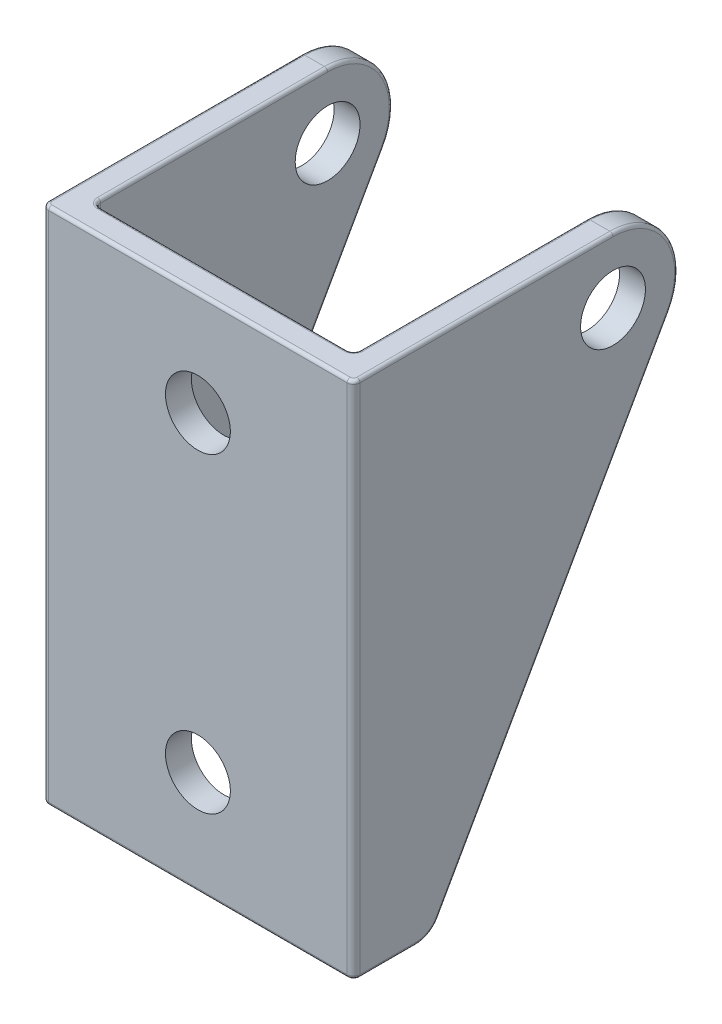
SolidWorks part; units mm, degrees
ref_plane "Front Plane" through (0, 0, 0) normal (0, 0, 1) x (1, 0, 0)
ref_plane "Top Plane" through (0, 0, 0) normal (0, 1, 0) x (1, 0, 0)
ref_plane "Right Plane" through (0, 0, 0) normal (1, 0, 0) x (0, 0, -1)
sketch "Sketch1" plane through (0, 0, 0) normal (0, 1, 0) x (1, 0, 0)
  line L0 (12, -1.5) -> (12, 23)
  line L1 (-11.5, -2) -> (11.5, -2)
  line L2 (-12, -1.5) -> (-12, 23)
  line L5 (12, 23) -> (10, 23)
  line L6 (10, 23) -> (10, 0.5)
  line L7 (9.5, 0) -> (-9.5, 0)
  line L8 (-10, 0.5) -> (-10, 23)
  line L9 (-10, 23) -> (-12, 23)
  line L10 (0, 0) -> (0, -2) construction
  arc A4 (11.5, -2) -> (12, -1.5) centre (11.5, -1.5) ccw
  arc A5 (10, 0.5) -> (9.5, 0) centre (9.5, 0.5) cw
  arc A6 (-9.5, 0) -> (-10, 0.5) centre (-9.5, 0.5) cw
  arc A7 (-11.5, -2) -> (-12, -1.5) centre (-11.5, -1.5) cw
  point P0 (0, 0)
  point P17 (12, 23)
  point P22 (12, -2)
  point P25 (10, 0)
  point P28 (-10, 0)
  point P36 (0, 0)
  dimension "D5" = 0.5
  dimension "D1" = 2
  dimension "D3" = 20
  dimension "D4" = 25
extrude "Boss-Extrude1" add sketch "Sketch1" along normal blind 40
sketch "Sketch2" plane through (-12, 0, 0) normal (-1, 0, 0) x (0, 0, 1)
  line L0 (-23, 40) -> (1.5, 40) construction
  line L1 (-22.3551, 32.5437) -> (-4.5739, 1.0175)
  line L4 (-23, 0) -> (1.5, 0) construction
  line L5 (-18, 40) -> (2, 40)
  line L6 (2, 40) -> (2, 0)
  line L7 (2, 0) -> (-2.8318, 0)
  line L10 (-23, 40) -> (-23, 0) construction
  arc A0 (-18, 40) -> (-22.3551, 32.5437) centre (-18, 35) ccw
  arc A1 (-4.5739, 1.0175) -> (-2.8318, 0) centre (-2.8318, 2) ccw
  point P19 (-4, 0)
  dimension "D1" = 5
  dimension "D3" = 2
  dimension "D2" = 6
extrude "Cut-Extrude1" cut sketch "Sketch2" against normal blind 30 flip side to cut
fillet "Fillet1" radius 0.25 32 edges at (10, 0, -1.6659) (-10, 0, -1.6659) (-9.8536, 0, -0.1464) (0, 0, 0) (12, 16.7806, -13.4645) (12, 37.5218, -22.3175) (12, 40, -8.25) (11.8536, 40, 1.8536) (0, 40, 2) (-11.8536, 40, 1.8536) (-12, 40, -8.25) (-12, 37.5218, -22.3175) (12, 0, -0.6659) (11.8536, 0, 1.8536) (0, 0, 2) (-11.8536, 0, 1.8536) (-10, 16.7806, -13.4645) (-10, 37.5218, -22.3175) (-10, 40, -9.25) (-9.8536, 40, -0.1464) (0, 40, 0) (10, 40, -9.25) (10, 37.5218, -22.3175) (9.8536, 40, -0.1464) (9.8536, 0, -0.1464) (-12, 16.7806, -13.4645) (-12, 0, -0.6659) (10, 16.7806, -13.4645) (-12, 0.273, -3.8405) (12, 0.273, -3.8405) (10, 0.273, -3.8405) (-10, 0.273, -3.8405)
sketch "Sketch3" plane through (-12, 0, 0) normal (-1, 0, 0) x (0, 0, 1)
  circle A0 centre (-18, 35) radius 2.5
  arc A2 (-18, 39.75) -> (-22.1373, 32.6665) centre (-18, 35) ccw construction
  dimension "D1" = 5
extrude "Cut-Extrude2" cut sketch "Sketch3" against normal blind 40 contours A0
sketch "Sketch4" plane through (0, 0, 0) normal (0, 0, -1) x (-1, 0, 0)
  line L0 (0, 32) -> (0, 40) construction
  line L1 (-9.5, 40) -> (9.5, 40) construction
  line L2 (0, 8) -> (0, 0) construction
  circle A0 centre (0, 32) radius 2.5
  circle A1 centre (0, 8) radius 2.5
  dimension "D1" = 5
  dimension "D2" = 8
extrude "Cut-Extrude3" cut sketch "Sketch4" against normal blind 30
equation "\"frontTubeLength\"= 1200mm"
equation "\"outDiameter\"= 35mm"
equation "\"keelOutDiameter\"= 1in"
equation "\"bottomTubeLength\"= \"frontTubeLength\"*0.9"
equation "\"frontShaftDiameter\"= 20mm"
equation "\"boltDiameter\"= 5mm"
equation "\"D1@Sketch3\"=\"boltDiameter\""
equation "\"D1@Sketch4\"=\"boltDiameter\""
